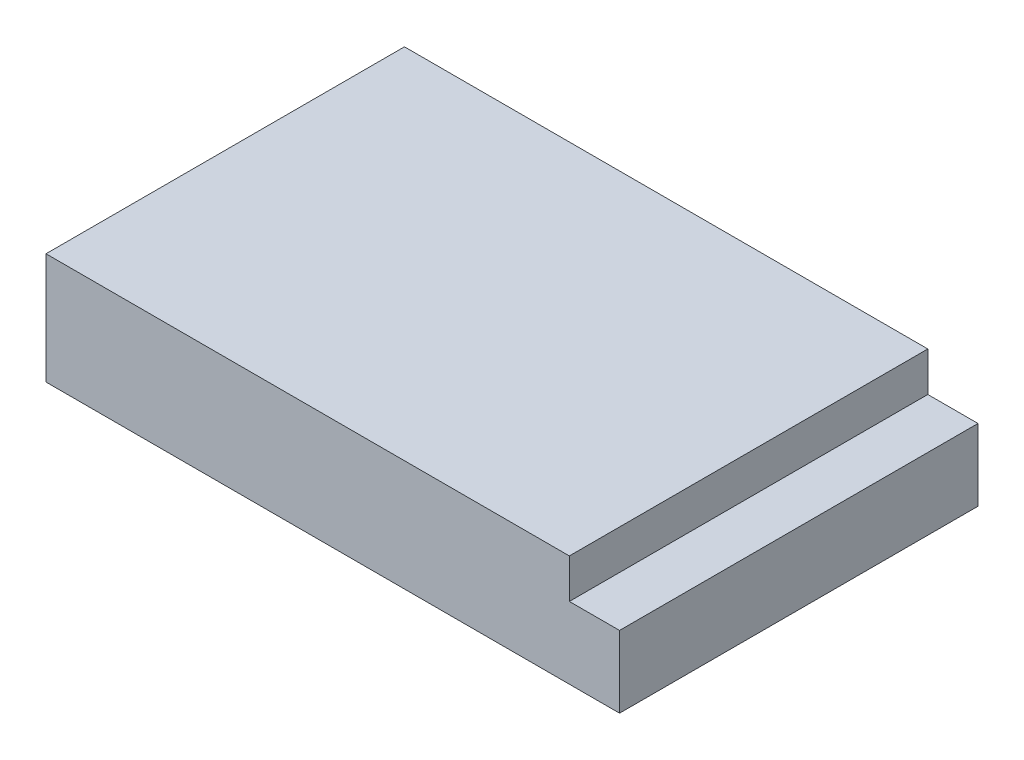
SolidWorks part; units mm, degrees
ref_plane "Plan de face" through (0, 0, 0) normal (0, 0, 1) x (1, 0, 0)
ref_plane "Plan de dessus" through (0, 0, 0) normal (0, 1, 0) x (1, 0, 0)
ref_plane "Plan de droite" through (0, 0, 0) normal (1, 0, 0) x (0, 0, -1)
sketch "Esquisse1" plane through (0, 0, 0) normal (0, 0, 1) x (1, 0, 0)
  line L0 (98.1487, 11) -> (98.1487, 0)
  line L1 (-47.8513, 11) -> (98.1487, 11)
  line L2 (-47.8513, 11) -> (-47.8513, -20)
  line L3 (-47.8513, -20) -> (112.1487, -20)
  line L4 (112.1487, 0) -> (112.1487, -20)
  line L5 (98.1487, 0) -> (112.1487, 0)
  dimension "D1" = 31
  dimension "D3" = 20
extrude "Boss.-Extru.1" add sketch "Esquisse1" along normal blind 100
